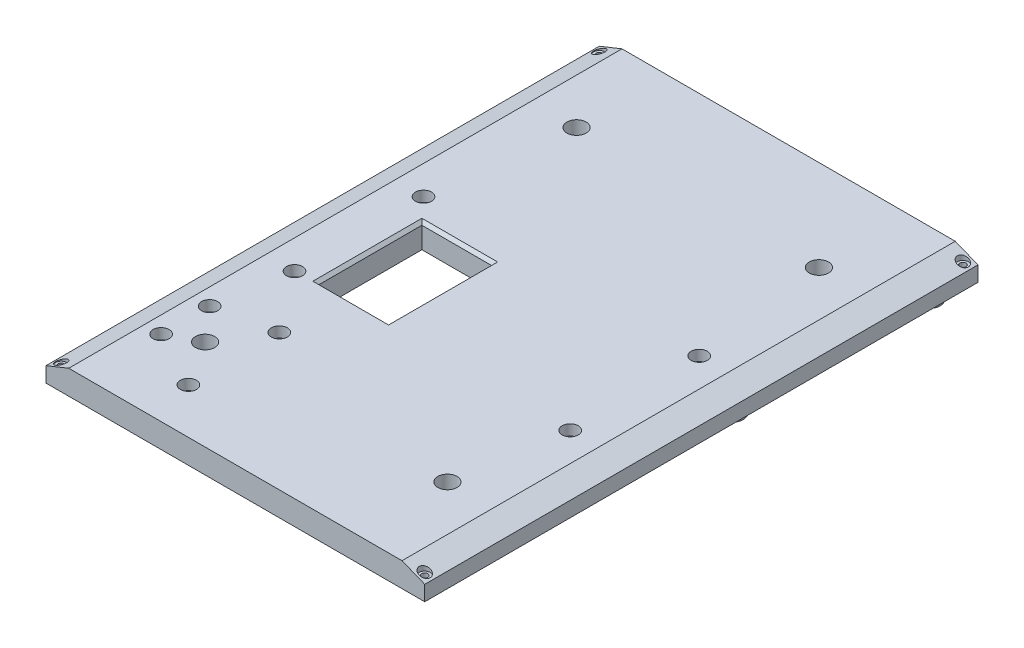
SolidWorks part; units mm, degrees
ref_plane "Ebene vorne" through (0, 0, 0) normal (0, 0, 1) x (1, 0, 0)
ref_plane "Ebene oben" through (0, 0, 0) normal (0, 1, 0) x (1, 0, 0)
ref_plane "Ebene rechts" through (0, 0, 0) normal (1, 0, 0) x (0, 0, -1)
sketch "Sketch1" plane through (0, 0, 0) normal (0, 0, 1) x (1, 0, 0)
  line L0 (0, 5) -> (7.5, 8)
  line L1 (0, 0) -> (125, 0)
  line L2 (0, 0) -> (0, 5)
  line L3 (0, 5) -> (125, 5) construction
  line L4 (125, 0) -> (125, 5)
  line L5 (125, 5) -> (117.5, 8)
  line L6 (7.5, 8) -> (117.5, 8)
  dimension "D1" = 125
  dimension "D2" = 5
  dimension "D3" = 3
  dimension "D4" = 7.5
  dimension "D5" = 3
  dimension "D6" = 7.5
extrude "Boss-Extrude1" add sketch "Sketch1" along normal blind 182.6
sketch "Sketch2" plane through (0, 0, 0) normal (0, -1, 0) x (1, 0, 0)
  line L1 (36.5, 176.6) -> (121.5, 176.6) construction
  line L2 (36.5, 176.6) -> (36.5, 120.6) construction
  line L3 (36.5, 120.6) -> (121.5, 120.6) construction
  line L4 (121.5, 176.6) -> (121.5, 120.6) construction
  line L5 (36.5, 148.6) -> (121.5, 148.6) construction
  line L6 (0, 182.6) -> (125, 182.6) construction
  line L7 (125, 182.6) -> (125, 0) construction
  circle A0 centre (40, 173.1) radius 0.85
  circle A1 centre (98, 173.1) radius 0.85
  circle A2 centre (40, 173.1) radius 2.5
  circle A3 centre (98, 173.1) radius 2.5
  circle A4 centre (98, 124.1) radius 2.5
  circle A5 centre (40, 124.1) radius 2.5
  circle A6 centre (98, 124.1) radius 0.85
  circle A7 centre (40, 124.1) radius 0.85
  dimension "D4" = 1.7
  dimension "D9" = 5
  dimension "D1" = 85
  dimension "D2" = 56
  dimension "D3" = 3.5
  dimension "D5" = 3.5
  dimension "D6" = 3.5
  dimension "D7" = 3.5
  dimension "D8" = 23.5
  dimension "D10" = 6
extrude "Boss-Extrude2" add sketch "Sketch2" along normal blind 3
sketch "Sketch3" plane through (0, 8, 0) normal (0, 1, 0) x (1, 0, 0)
  line L0 (62.5, 0) -> (62.5, -95.9866) construction
  line L1 (117.5, 0) -> (7.5, 0) construction
  line L2 (0, -152.6) -> (125, -152.6) construction
  line L3 (0, -182.6) -> (0, 0) construction
  line L4 (125, -182.6) -> (125, 0) construction
  line L5 (117.5, -182.6) -> (7.5, -182.6) construction
  line L6 (0, -91.3) -> (125, -91.3) construction
  circle A0 centre (22.5, -152.6) radius 3.175
  circle A1 centre (102.5, -152.6) radius 3.175
  circle A2 centre (102.5, -30) radius 3.175
  circle A3 centre (22.5, -30) radius 3.175
  dimension "D2" = 6.35
  dimension "D3" = 40
  dimension "D1" = 30
  dimension "D4" = 40
extrude "Cut-Extrude1" cut sketch "Sketch3" against normal blind 15
sketch "Sketch4" plane through (0, 0, 0) normal (0, -1, 0) x (1, 0, 0)
  line L0 (0, 182.6) -> (125, 0) construction
  line L2 (56.15, 81.14) -> (68.85, 81.14) construction
  line L3 (56.15, 81.14) -> (56.15, 101.46) construction
  line L4 (56.15, 101.46) -> (68.85, 101.46) construction
  line L5 (68.85, 81.14) -> (68.85, 101.46) construction
  line L6 (56.15, 81.14) -> (68.85, 101.46) construction
  line L7 (56.15, 101.46) -> (68.85, 81.14) construction
  circle A0 centre (56.15, 101.46) radius 1.55
  circle A1 centre (68.85, 101.46) radius 1.55
  circle A2 centre (68.85, 81.14) radius 1.55
  circle A3 centre (56.15, 81.14) radius 1.55
  circle A4 centre (56.15, 81.14) radius 2.6
  circle A5 centre (68.85, 81.14) radius 2.6
  circle A6 centre (68.85, 101.46) radius 2.6
  circle A7 centre (56.15, 101.46) radius 2.6
  point P4 (62.5, 91.3)
  dimension "D3" = 3.1
  dimension "D4" = 5.2
  dimension "D1" = 20.32
  dimension "D2" = 12.7
extrude "Boss-Extrude3" add sketch "Sketch4" along normal blind 6
sketch "Sketch7" plane through (0, 8, 0) normal (0, 1, 0) x (1, 0, 0)
  line L0 (17, 0) -> (17, -182.6) construction
  line L1 (117.5, 0) -> (7.5, 0) construction
  line L2 (117.5, -182.6) -> (7.5, -182.6) construction
  line L3 (0, -182.6) -> (0, 0) construction
  line L4 (108, 0) -> (108, -182.6) construction
  line L5 (125, -182.6) -> (125, 0) construction
  circle A0 centre (17, -75.01) radius 1.6
  circle A1 centre (17, -117.585) radius 1.6
  circle A2 centre (108, -75.01) radius 1.6
  circle A3 centre (108, -117.59) radius 1.6
  point P12 (17, -91.3)
  point P21 (108, -91.3)
  dimension "D4" = 3.2
  dimension "D5" = 3.2
  dimension "D9" = 3.2
  dimension "D10" = 3.2
  dimension "D1" = 17
  dimension "D2" = 26.285
  dimension "D3" = 16.29
  dimension "D6" = 17
  dimension "D7" = 16.29
  dimension "D8" = 26.29
extrude "Cut-Extrude3" cut sketch "Sketch7" against normal blind 10
sketch "Sketch8" plane through (0, 8, 0) normal (0, 1, 0) x (1, 0, 0)
  line L0 (13, -182.6) -> (13, 0) construction
  line L1 (117.5, -182.6) -> (7.5, -182.6) construction
  line L2 (117.5, 0) -> (7.5, 0) construction
  line L3 (0, -182.6) -> (0, 0) construction
  circle A0 centre (13, -141.6) radius 1.6
  circle A1 centre (13, -157.6) radius 1.6
  circle A2 centre (17, -117.585) radius 1.6 construction
  dimension "D2" = 16
  dimension "D1" = 13
  dimension "D3" = 25
extrude "Cut-Extrude4" cut sketch "Sketch8" against normal blind 10
sketch "Sketch6" plane through (0, 0, 0) normal (0, -1, 0) x (1, 0, 0)
  line L1 (22.4076, 118.2462) -> (48.4076, 118.2462) construction
  line L2 (22.4076, 118.2462) -> (22.4076, 71.2462) construction
  line L3 (22.4076, 71.2462) -> (48.4076, 71.2462) construction
  line L4 (48.4076, 118.2462) -> (48.4076, 71.2462) construction
  circle A0 centre (22.4076, 118.2462) radius 0.85
  circle A1 centre (48.4076, 118.2462) radius 0.85
  circle A2 centre (48.4076, 71.2462) radius 0.85
  circle A3 centre (22.4076, 71.2462) radius 0.85
  dimension "D3" = 1.7
  dimension "D1" = 47
  dimension "D2" = 26
extrude "Cut-Extrude2" cut sketch "Sketch6" against normal blind 7
sketch "Sketch9" plane through (0, 0, 0) normal (0, -1, 0) x (1, 0, 0)
  line L17 (34, 73) -> (117, 73) construction
  line L18 (34, 73) -> (34, 8) construction
  line L19 (34, 8) -> (117, 8) construction
  line L20 (117, 73) -> (117, 8) construction
  line L25 (125, 182.6) -> (125, 0) construction
  line L33 (0, 0) -> (125, 0) construction
  circle A0 centre (34, 73) radius 1.95
  circle A1 centre (117, 73) radius 1.95
  circle A2 centre (117, 8) radius 1.95
  circle A3 centre (34, 8) radius 1.95
  circle A14 centre (117, 73) radius 3.5
  circle A15 centre (117, 8) radius 3.5
  circle A16 centre (34, 8) radius 3.5
  circle A17 centre (34, 73) radius 3.5
  point P6 (-66.3551, 38.5)
  dimension "D6" = 3.9
  dimension "D3" = 7
  dimension "D1" = 83
  dimension "D2" = 65
  dimension "D4" = 8
  dimension "D11" = 8
extrude "Boss-Extrude4" add sketch "Sketch9" along normal blind 5
sketch "Sketch10" plane through (0, 8, 0) normal (0, 1, 0) x (1, 0, 0)
  line L0 (32, -167.6) -> (32, -137.6) construction
  line L1 (0, -182.6) -> (0, 0) construction
  line L2 (117.5, -182.6) -> (7.5, -182.6) construction
  circle A0 centre (32, -137.6) radius 1.6
  circle A1 centre (32, -167.6) radius 1.6
  dimension "D2" = 3.2
  dimension "D3" = 3.2
  dimension "D1" = 30
  dimension "D4" = 32
  dimension "D5" = 15
extrude "Cut-Extrude5" cut sketch "Sketch10" against normal blind 10
sketch "Sketch11" plane through (0, 0, 0) normal (0, -1, 0) x (1, 0, 0)
  line L0 (22.4076, 118.2462) -> (48.4076, 118.2462) construction
  line L1 (35.4076, 118.2462) -> (35.4076, 90.0894) construction
  line L3 (23.9076, 116.4462) -> (46.9076, 116.4462)
  line L4 (23.9076, 116.4462) -> (23.9076, 82.4462)
  line L5 (23.9076, 82.4462) -> (46.9076, 82.4462)
  line L6 (46.9076, 116.4462) -> (46.9076, 82.4462)
  line L7 (23.9076, 116.4462) -> (46.9076, 82.4462) construction
  line L8 (23.9076, 82.4462) -> (46.9076, 116.4462) construction
  point P6 (35.4076, 99.4462)
  dimension "D1" = 23
  dimension "D2" = 34
  dimension "D3" = 1.8
extrude "Cut-Extrude6" cut sketch "Sketch11" against normal blind 10
chamfer "Chamfer1" distance 1 angle 45 4 edges at (35.4076, 8, 116.4462) (23.9076, 8, 99.4462) (46.9076, 8, 99.4462) (35.4076, 8, 82.4462)
sketch "Sketch12" plane through (0, 8, 0) normal (0, 1, 0) x (1, 0, 0)
  circle A0 centre (17, -75.01) radius 2.65
  circle A1 centre (108, -75.01) radius 2.65
  circle A2 centre (108, -117.59) radius 2.65
  circle A3 centre (32, -137.6) radius 2.65
  circle A4 centre (32, -167.6) radius 2.65
  circle A5 centre (13, -157.6) radius 2.65
  circle A6 centre (13, -141.6) radius 2.65
  circle A7 centre (17, -117.585) radius 2.65
  dimension "D1" = 5.3
extrude "Cut-Extrude7" cut sketch "Sketch12" against normal blind 3.5
sketch "Sketch13" plane through (0, 8, 0) normal (0, 1, 0) x (1, 0, 0)
  line L0 (0, -2.5) -> (125, -2.5) construction
  line L1 (0, -182.6) -> (0, 0) construction
  line L2 (125, -182.6) -> (125, 0) construction
  line L3 (0, -180.1) -> (125, -180.1) construction
  line L4 (117.5, 0) -> (7.5, 0) construction
  line L5 (117.5, -182.6) -> (7.5, -182.6) construction
  line L6 (2.5, -2.5) -> (2.5, -180.1) construction
  line L7 (122.5, 0) -> (122.5, -182.6) construction
  circle A0 centre (2.5, -180.1) radius 1.05
  circle A1 centre (122.5, -180.1) radius 1.05
  circle A2 centre (122.5, -2.5) radius 1.05
  circle A3 centre (2.5, -2.5) radius 1.05
  dimension "D5" = 2.1
  dimension "D1" = 2.5
  dimension "D2" = 2.5
  dimension "D3" = 2.5
  dimension "D4" = 2.5
extrude "Cut-Extrude8" cut sketch "Sketch13" against normal blind 8
sketch "Sketch15" plane through (0, 8, 0) normal (0, 1, 0) x (1, 0, 0)
  circle A0 centre (2.5, -180.1) radius 1.8
  circle A1 centre (2.5, -2.5) radius 1.8
  circle A2 centre (122.5, -2.5) radius 1.8
  circle A3 centre (122.5, -180.1) radius 1.8
  dimension "D1" = 3.6
extrude "Cut-Extrude9" cut sketch "Sketch15" against normal blind 3
